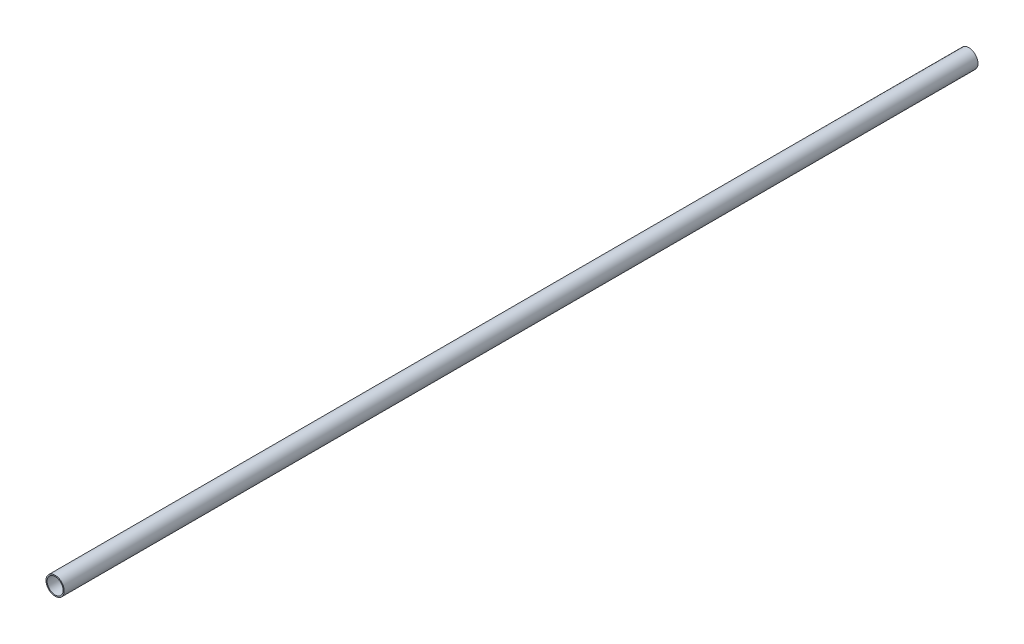
SolidWorks part; units mm, degrees
ref_plane "Plan de face" through (0, 0, 0) normal (0, 0, 1) x (1, 0, 0)
ref_plane "Plan de dessus" through (0, 0, 0) normal (0, 1, 0) x (1, 0, 0)
ref_plane "Plan de droite" through (0, 0, 0) normal (1, 0, 0) x (0, 0, -1)
sketch "Esquisse1" plane through (0, 0, 0) normal (0, 0, 1) x (1, 0, 0)
  circle A0 centre (0, 0) radius 4
  circle A1 centre (0, 0) radius 3.5
  dimension "D1" = 8
  dimension "D2" = 7
extrude "Boss.-Extru.1" add sketch "Esquisse1" along normal blind 400
